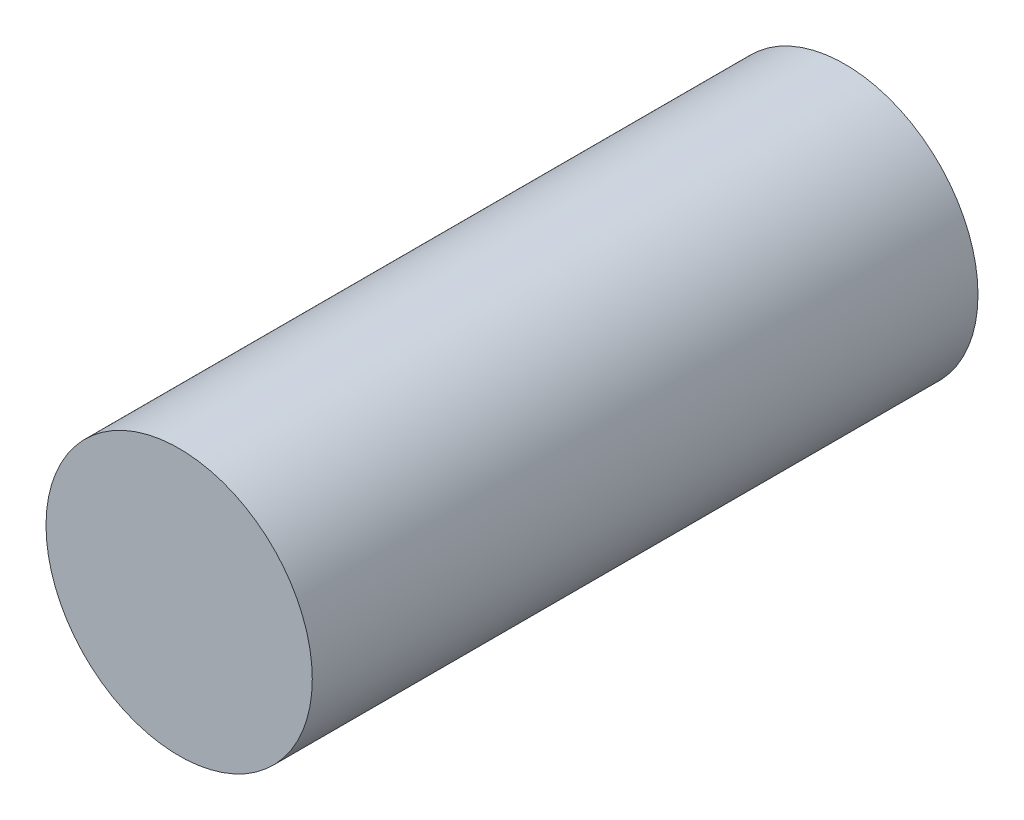
SolidWorks part; units mm, degrees
ref_plane "Front" through (0, 0, 0) normal (0, 0, 1) x (1, 0, 0)
ref_plane "Top" through (0, 0, 0) normal (0, 1, 0) x (1, 0, 0)
ref_plane "Right" through (0, 0, 0) normal (1, 0, 0) x (0, 0, -1)
sketch "Sketch1" plane through (0, 0, 0) normal (0, 0, 1) x (1, 0, 0)
  circle A0 centre (0, 0) radius 1
  dimension "D1" = 2
extrude "Boss-Extrude1" add sketch "Sketch1" along normal blind 5
